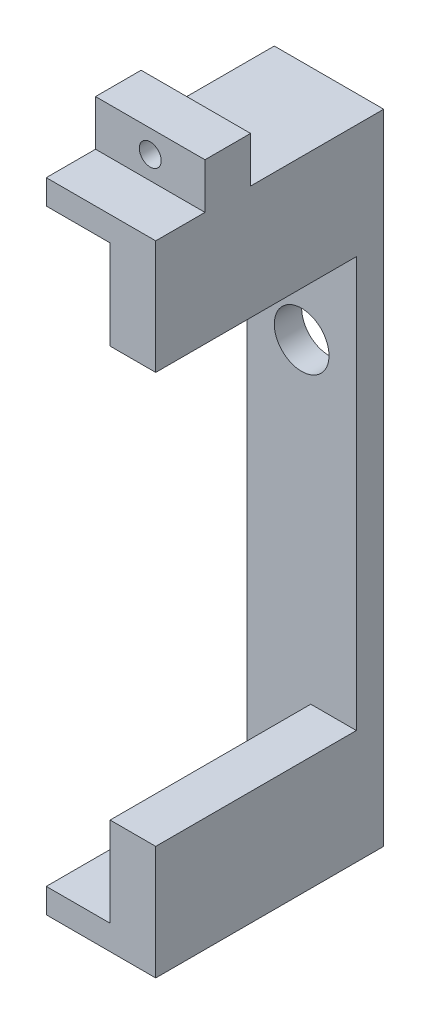
SolidWorks part; units mm, degrees
ref_plane "Alzado" through (0, 0, 0) normal (0, 0, 1) x (1, 0, 0)
ref_plane "Planta" through (0, 0, 0) normal (0, 1, 0) x (1, 0, 0)
ref_plane "Vista lateral" through (0, 0, 0) normal (1, 0, 0) x (0, 0, -1)
sketch "Croquis1" plane through (0, 0, 0) normal (0, 0, 1) x (1, 0, 0)
  line L1 (-3, -17.5) -> (3, -17.5)
  line L2 (-3, -17.5) -> (-3, 17.5)
  line L3 (-3, 17.5) -> (3, 17.5)
  line L4 (3, -17.5) -> (3, 17.5)
  line L5 (-3, -17.5) -> (3, 17.5) construction
  line L6 (-3, 17.5) -> (3, -17.5) construction
  point P0 (0, 0)
  dimension "D1" = 35
  dimension "D2" = 6
extrude "Saliente-Extruir1" add sketch "Croquis1" along normal blind 12.5
sketch "Croquis2" plane through (0, 0, 12.5) normal (0, 0, 1) x (1, 0, 0)
  line L0 (3, 11.25) -> (-3, 11.25)
  line L1 (3, -17.5) -> (3, 17.5) construction
  line L2 (-3, 17.5) -> (-3, -17.5) construction
  line L4 (-3, -11.25) -> (3, -11.25)
  line L6 (-3, 11.25) -> (-3, -11.25)
  line L7 (3, -11.25) -> (3, 11.25)
  line L8 (3, 0) -> (0, 0) construction
  dimension "D1" = 22.5
extrude "Cortar-Extruir1" cut sketch "Croquis2" against normal offset from surface (11 mm away) 1.5 up to face at (0, 0, 0)
sketch "Croquis3" plane through (0, 0, 0) normal (0, 0, -1) x (-1, 0, 0)
  line L0 (0, 17.5) -> (0, 5.8) construction
  line L1 (-3, 17.5) -> (3, 17.5) construction
  circle A0 centre (0, 5.8) radius 1.5
  dimension "D1" = 3
  dimension "D2" = 11.7
extrude "Cortar-Extruir2" cut sketch "Croquis3" against normal through all both and the other way through all
sketch "Croquis4" plane through (0, 0, 12.5) normal (0, 0, 1) x (1, 0, 0)
  line L0 (-3, 11.25) -> (0.5, 11.25)
  line L1 (3, 11.25) -> (-3, 11.25) construction
  line L2 (0.5, 11.25) -> (0.5, 16.15)
  line L3 (0.5, 16.15) -> (-3, 16.15)
  line L5 (0, 0) -> (-11.3278, 0) construction
  line L6 (0.5, -16.15) -> (-3, -16.15)
  line L7 (0.5, -11.25) -> (0.5, -16.15)
  line L8 (-3, -11.25) -> (0.5, -11.25)
  line L9 (-3, 16.15) -> (-3, 11.25)
  line L10 (-3, -16.15) -> (-3, -11.25)
  line L11 (-3, 17.5) -> (-3, 11.25) construction
  line L12 (-3, 11.25) -> (-3, -11.25) construction
  dimension "D1" = 3.5
  dimension "D2" = 4.9
extrude "Cortar-Extruir3" cut sketch "Croquis4" against normal blind 11 and the other way through all
sketch "Croquis5" plane through (0, 17.5, 0) normal (0, -1, 0) x (1, 0, 0)
  line L0 (-3, 12.5) -> (-3, 0) construction
  line L1 (-3, 7.3) -> (3, 7.3)
  line L2 (-3, 7.3) -> (-3, 9.8)
  line L3 (-3, 9.8) -> (3, 9.8)
  line L4 (3, 7.3) -> (3, 9.8)
  line L5 (3, 12.5) -> (3, 0) construction
  line L6 (-3, 0) -> (3, 0) construction
  dimension "D1" = 7.3
  dimension "D2" = 2.5
extrude "Saliente-Extruir2" add sketch "Croquis5" against normal blind 2.5
sketch "Croquis6" plane through (0, 0, 9.8) normal (0, 0, 1) x (1, 0, 0)
  line L0 (0, 17.5) -> (0, 18.75) construction
  line L1 (3, 17.5) -> (-3, 17.5) construction
  line L2 (0, 18.75) -> (3, 18.75) construction
  line L3 (3, 20) -> (3, 17.5) construction
  circle A0 centre (0, 18.75) radius 0.6
  dimension "D1" = 1.2
extrude "Cortar-Extruir4" cut sketch "Croquis6" against normal through all both and the other way through all
